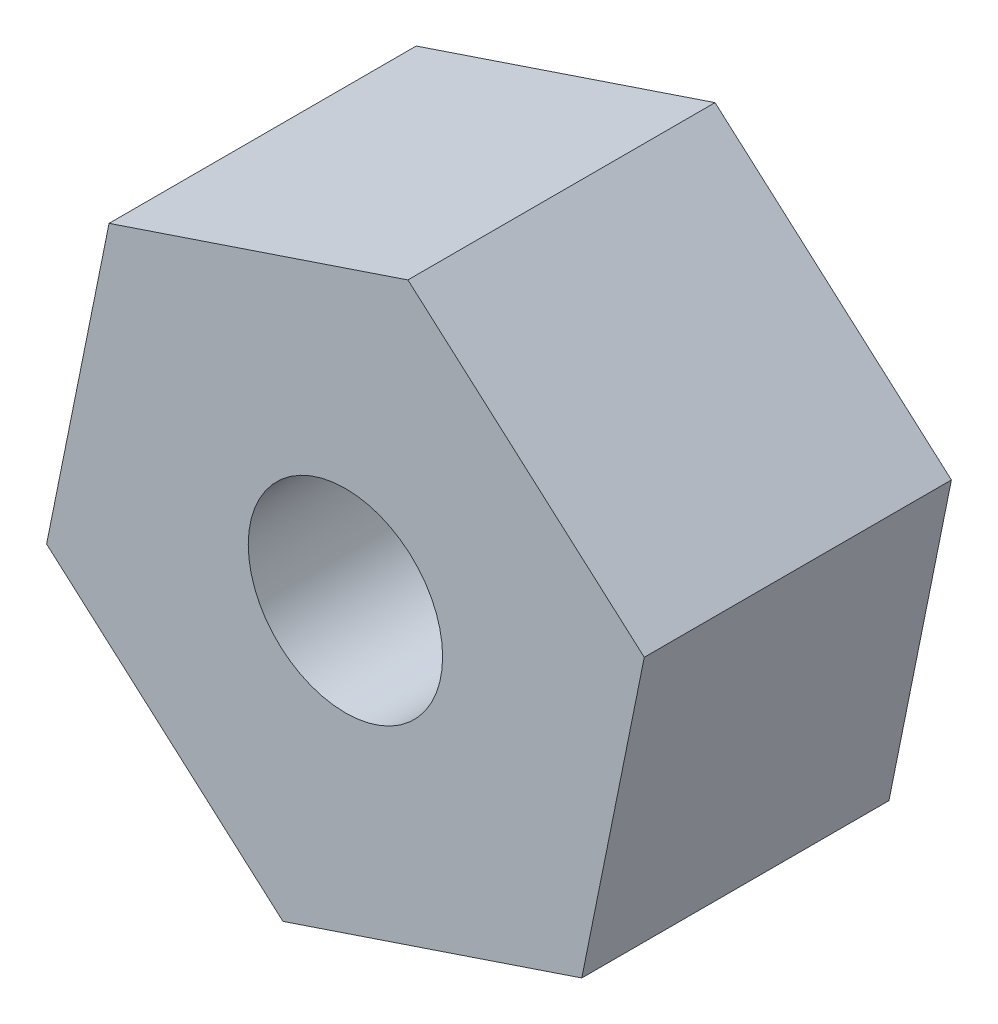
SolidWorks part; units mm, degrees
ref_plane "Front Plane" through (0, 0, 0) normal (0, 0, 1) x (1, 0, 0)
ref_plane "Top Plane" through (0, 0, 0) normal (0, 1, 0) x (1, 0, 0)
ref_plane "Right Plane" through (0, 0, 0) normal (1, 0, 0) x (0, 0, -1)
sketch "Sketch1" plane through (0, 0, 0) normal (0, 0, 1) x (1, 0, 0)
  line L1 (3.4753, 1.1676) -> (0.7265, 3.5935)
  line L2 (0.7265, 3.5935) -> (-2.7488, 2.4259)
  line L3 (-2.7488, 2.4259) -> (-3.4753, -1.1676)
  line L4 (-3.4753, -1.1676) -> (-0.7265, -3.5935)
  line L5 (-0.7265, -3.5935) -> (2.7488, -2.4259)
  line L6 (2.7488, -2.4259) -> (3.4753, 1.1676)
  circle A0 centre (0, 0) radius 3.175 construction
  circle A1 centre (0, 0) radius 1.1303
extrude "Extrude1" add sketch "Sketch1" along normal blind 3.5719
